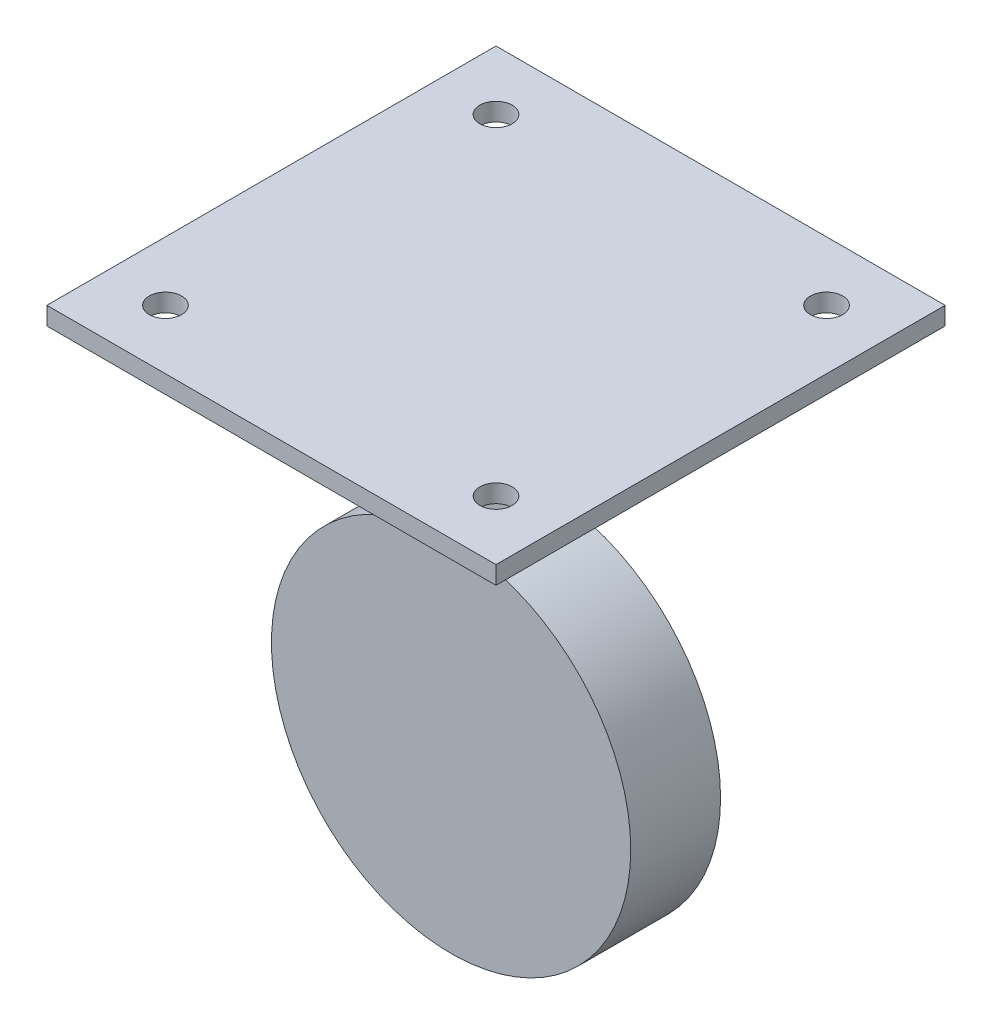
SolidWorks part; units mm, degrees
ref_plane "前视基准面" through (0, 0, 0) normal (0, 0, 1) x (1, 0, 0)
ref_plane "上视基准面" through (0, 0, 0) normal (0, 1, 0) x (1, 0, 0)
ref_plane "右视基准面" through (0, 0, 0) normal (1, 0, 0) x (0, 0, -1)
sketch "草图1" plane through (0, 0, 0) normal (0, 0, 1) x (1, 0, 0)
  circle A0 centre (0, 0) radius 20
  dimension "D1" = 40
extrude "凸台-拉伸1" add sketch "草图1" along normal mid plane 10
sketch "草图2" plane through (0, 0, 0) normal (0, 0, 1) x (1, 0, 0)
  line L0 (0, 0) -> (0, 40) construction
  line L1 (5, 0) -> (5, 40)
  line L2 (-5, 0) -> (-5, 40)
  line L3 (-5, 40) -> (5, 40)
  line L4 (-5, 0) -> (5, 0)
  circle A0 centre (0, 0) radius 20 construction
  circle A1 centre (0, 0) radius 20
  dimension "D3" = 60
  dimension "D1" = 5
  dimension "D2" = 5
extrude "凸台-拉伸2" add sketch "草图2" along normal mid plane 5 contours L0 A1 L1 L3 | A1 L0 L3 L2
sketch "草图3" plane through (0, 40, 0) normal (0, 1, 0) x (1, 0, 0)
  line L1 (25, -25) -> (-25, -25)
  line L2 (25, -25) -> (25, 25)
  line L3 (25, 25) -> (-25, 25)
  line L4 (-25, -25) -> (-25, 25)
  line L5 (25, -25) -> (-25, 25) construction
  line L6 (25, 25) -> (-25, -25) construction
  circle A0 centre (-18.4, 18.4) radius 1.8
  circle A1 centre (18.4, 18.4) radius 1.8
  circle A2 centre (18.4, -18.4) radius 1.8
  circle A3 centre (-18.4, -18.4) radius 1.8
  point P0 (0, 0)
  point P17 (0, 0)
  dimension "D3" = 50
  dimension "D4" = 3.6
  dimension "D1" = 36.8
  dimension "D2" = 4
extrude "凸台-拉伸3" add sketch "草图3" against normal blind 2
